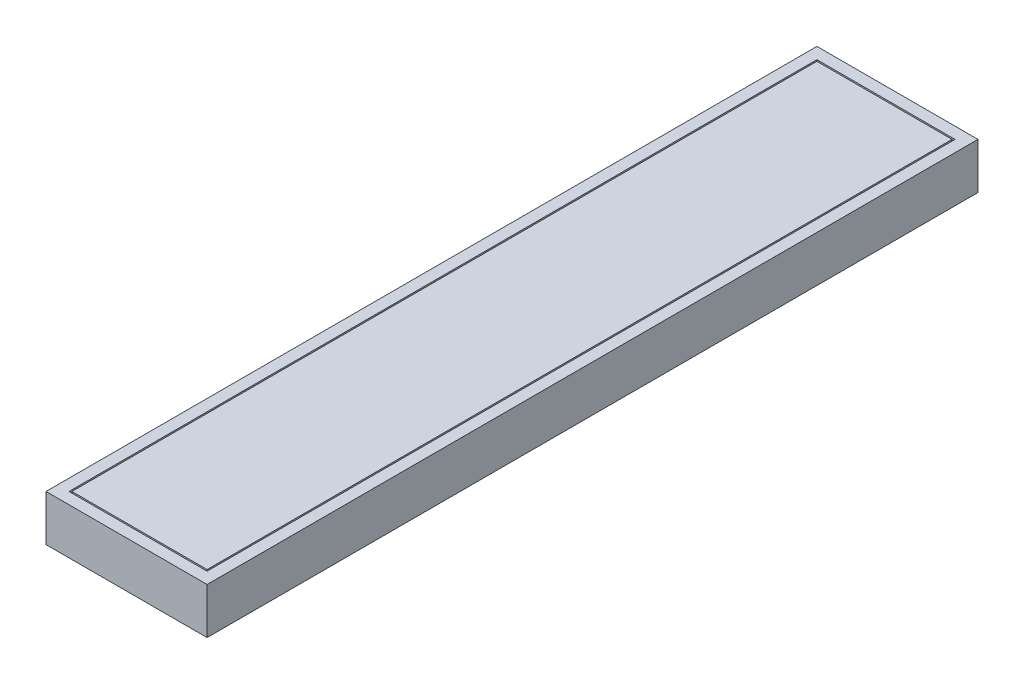
SolidWorks part; units mm, degrees
ref_plane "Front Plane" through (0, 0, 0) normal (0, 0, 1) x (1, 0, 0)
ref_plane "Top Plane" through (0, 0, 0) normal (0, 1, 0) x (1, 0, 0)
ref_plane "Right Plane" through (0, 0, 0) normal (1, 0, 0) x (0, 0, -1)
ref_plane "Plane1" through (0, -60, 0) normal (0, -1, 0) x (1, 0, 0)
sketch "Sketch1" plane through (0, -60, 0) normal (0, -1, 0) x (1, 0, 0)
  line L0 (-140, 0) -> (140, 0)
  line L1 (140, 0) -> (140, 1340)
  line L2 (140, 1340) -> (-140, 1340)
  line L3 (-140, 1340) -> (-140, 0)
  dimension "D1" = 1340
  dimension "D2" = 280
  dimension "D3" = 140
extrude "Boss-Extrude1" add sketch "Sketch1" against normal blind 80
sketch "Sketch2" plane through (0, 20, 0) normal (0, 1, 0) x (-1, 0, 0)
  line L0 (120, 1320) -> (-120, 1320)
  line L1 (-120, 1320) -> (-120, 20)
  line L2 (-120, 20) -> (120, 20)
  line L3 (120, 20) -> (120, 1320)
  dimension "D1" = 20
  dimension "D2" = 1300
  dimension "D3" = 240
  dimension "D4" = 120
extrude "Cut-Extrude1" cut sketch "Sketch2" against normal blind 11
sketch "Sketch3" plane through (0, 9, 0) normal (0, 1, 0) x (-1, 0, 0)
  line L0 (117.5, 1317.5) -> (117.5, 22.5)
  line L1 (117.5, 22.5) -> (-117.5, 22.5)
  line L2 (-117.5, 22.5) -> (-117.5, 1317.5)
  line L3 (-117.5, 1317.5) -> (117.5, 1317.5)
  line L4 (-120, 20) -> (120, 20) construction
  line L5 (120, 20) -> (120, 1320) construction
  dimension "D1" = 2.5
  dimension "D2" = 2.5
  dimension "D3" = 235
  dimension "D4" = 1295
extrude "Boss-Extrude2" add sketch "Sketch3" along normal blind 11
